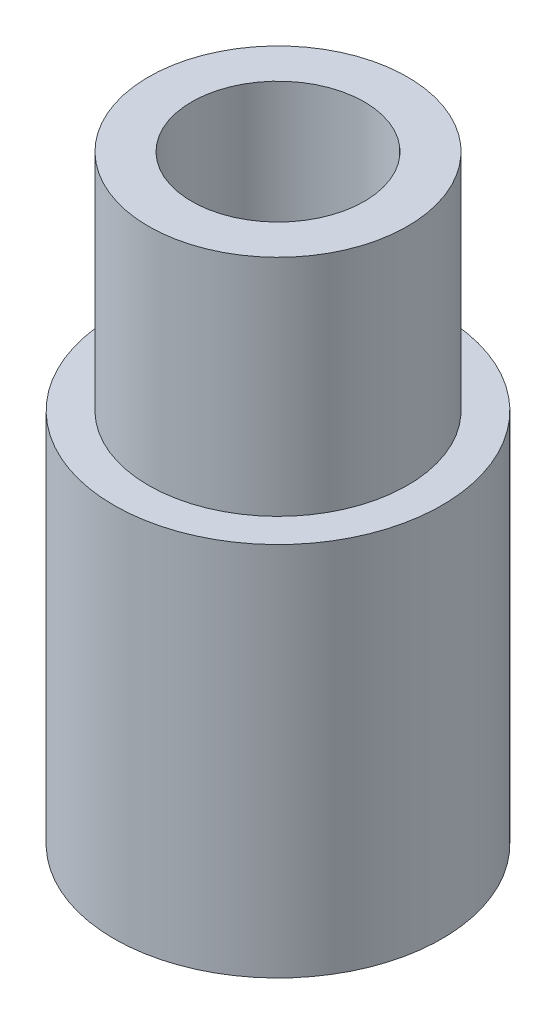
SolidWorks part; units mm, degrees
ref_plane "Front Plane" through (0, 0, 0) normal (0, 0, 1) x (1, 0, 0)
ref_plane "Top Plane" through (0, 0, 0) normal (0, 1, 0) x (1, 0, 0)
ref_plane "Right Plane" through (0, 0, 0) normal (1, 0, 0) x (0, 0, -1)
sketch "Sketch1" plane through (0, 0, 0) normal (0, 1, 0) x (1, 0, 0)
  circle A0 centre (0, 0) radius 1.9
  dimension "D1" = 3.8
extrude "Boss-Extrude1" add sketch "Sketch1" along normal blind 6.95
sketch "Sketch2" plane through (0, 6.95, 0) normal (0, 1, 0) x (1, 0, 0)
  circle A0 centre (0, 0) radius 1.5
  dimension "D1" = 3
extrude "Cut-Extrude1" cut sketch "Sketch2" against normal offset from surface (2.6 mm away) 4.35 flip side to cut up to face at (0, 0, 1.9)
sketch "Sketch3" plane through (0, 0, 0) normal (0, -1, 0) x (1, 0, 0)
  circle A0 centre (0, 0) radius 1
  dimension "D1" = 2
extrude "Cut-Extrude2" cut sketch "Sketch3" against normal through all
